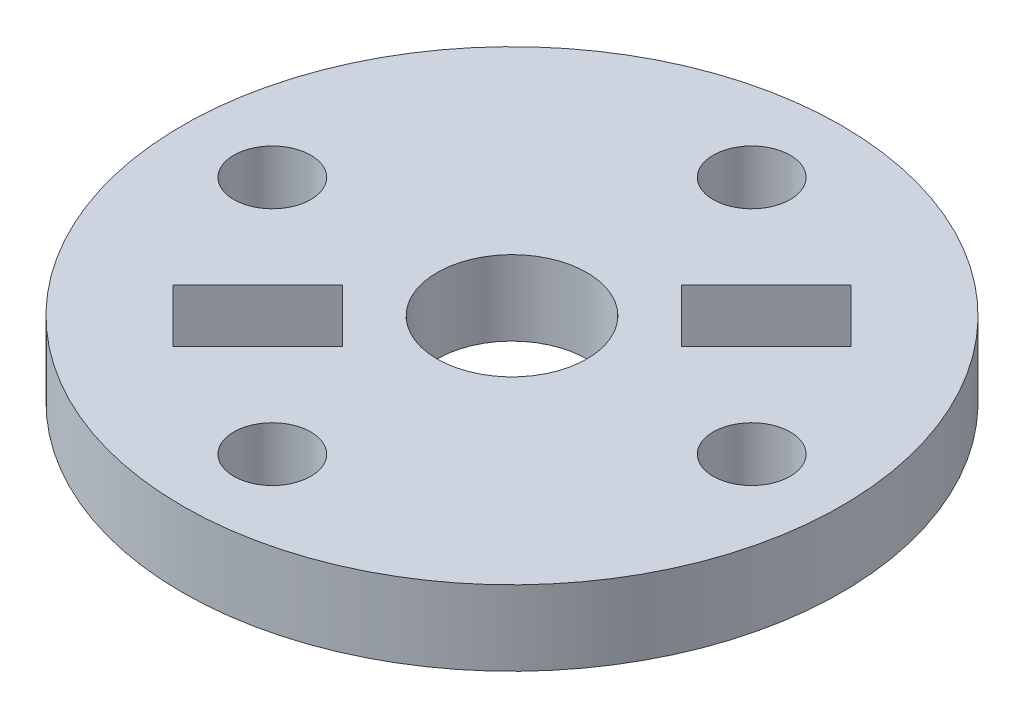
SolidWorks part; units mm, degrees
ref_plane "Front Plane" through (0, 0, 0) normal (0, 0, 1) x (1, 0, 0)
ref_plane "Top Plane" through (0, 0, 0) normal (0, 1, 0) x (1, 0, 0)
ref_plane "Right Plane" through (0, 0, 0) normal (1, 0, 0) x (0, 0, -1)
sketch "Sketch1" plane through (0, 0, 0) normal (0, 1, 0) x (1, 0, 0)
  circle A0 centre (0, 0) radius 13.97
  dimension "D1" = 27.94
extrude "Boss-Extrude1" add sketch "Sketch1" along normal blind 3.175
sketch "Sketch2" plane through (0, 3.175, 0) normal (0, 1, 0) x (1, 0, 0)
  circle A0 centre (0, 0) radius 3.175
  dimension "D1" = 6.35
extrude "Cut-Extrude1" cut sketch "Sketch2" against normal blind 3.175
sketch "Sketch3" plane through (0, 3.175, 0) normal (0, 1, 0) x (1, 0, 0)
  line L0 (0, 0) -> (13.6121, 0)
  line L1 (0, 0) -> (5.3882, 5.3882)
  dimension "D1" = 45
  dimension "D2" = 7.62
hole_wizard "#4 Clearance Hole1" positions "Sketch5" profile "Sketch4" hole size "#4" standard "ANSI Inch"
sketch "Sketch5" plane through (0, 3.175, 0) normal (0, 1, 0) x (1, 0, 0)
  point P0 (0, 10.16)
  dimension "D1" = 10.16
sketch "Sketch4" plane through (0, 3.175, -10.16) normal (1, 0, 0) x (0, 0, 1)
  line L0 (0, 0) -> (0, 11.1406)
  line L1 (0, 11.1406) -> (1.6319, 10.16)
  line L2 (1.6319, 10.16) -> (1.6319, 0)
  line L5 (1.6319, 0) -> (0, 0)
  line L10 (0, 11.1406) -> (-1.632, 10.16) construction
  line L11 (0, -6.35) -> (0, 107.95) construction
  dimension "Hole Dia." = 3.2639
  dimension "Hole Depth" = 10.16
  dimension "Drill Angle" = 118
pattern_circular "CirPattern1" count 4 over 360 about axis through (0, 0, 0) along (0, 1, 0) of "#4 Clearance Hole1"
sketch "Sketch6" plane through (0, 3.175, 0) normal (0, 1, 0) x (1, 0, 0)
  line L0 (4.7146, 2.4696) -> (8.3067, 6.0617)
  line L1 (4.7146, 2.4696) -> (2.4696, 4.7146)
  line L2 (8.3067, 6.0617) -> (6.0617, 8.3067)
  line L3 (2.4696, 4.7146) -> (6.0617, 8.3067)
  line L4 (4.7146, 2.4696) -> (6.0617, 8.3067) construction
  line L5 (8.3067, 6.0617) -> (2.4696, 4.7146) construction
  line L6 (0, 0) -> (5.3882, 5.3882) construction
  point P1 (5.3882, 5.3882)
  dimension "D1" = 180
  dimension "D2" = 5.08
  dimension "D3" = 3.175
extrude "Cut-Extrude2" cut sketch "Sketch6" against normal blind 5.08
pattern_circular "CirPattern2" count 2 over 360 about axis through (0, 0, 0) along (0, 1, 0) of "Cut-Extrude2"
